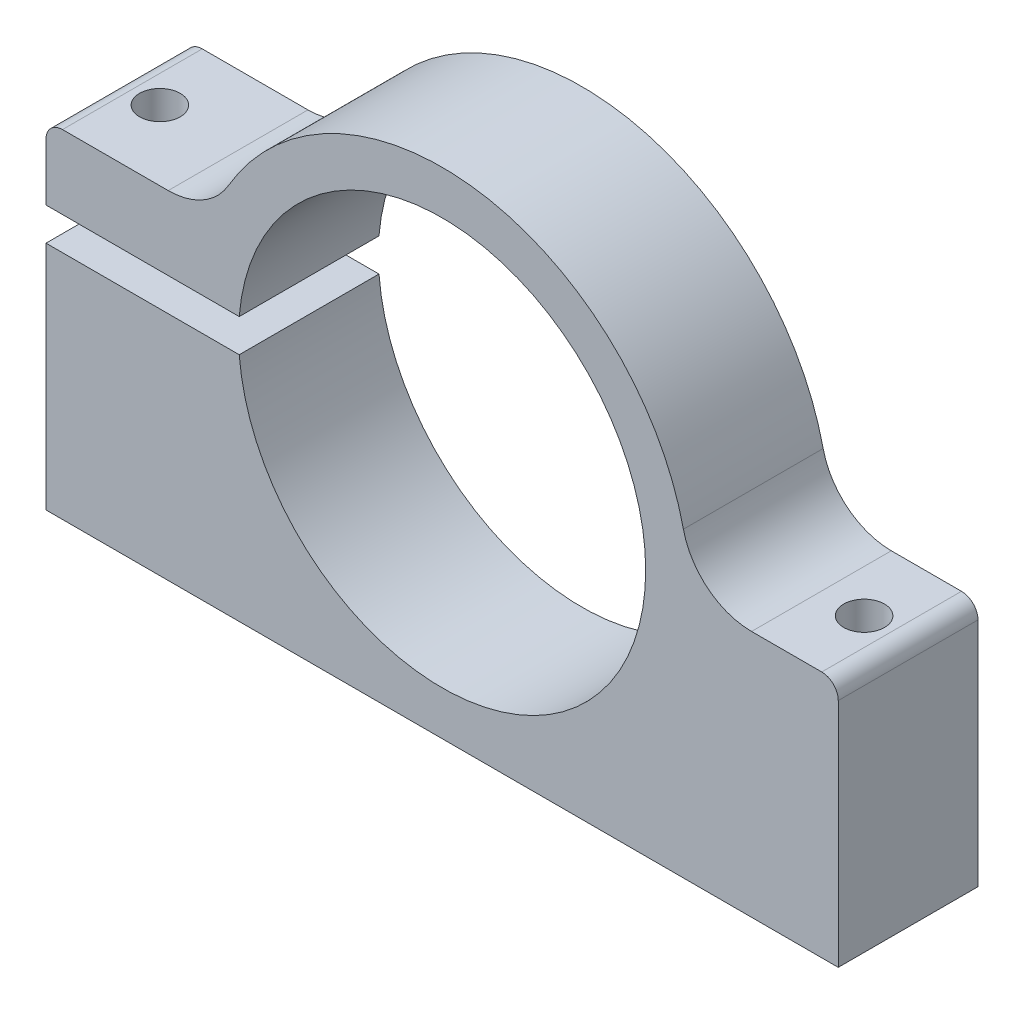
SolidWorks part; units mm, degrees
material "6061 Alloy"
ref_plane "Front Plane" through (0, 0, 0) normal (0, 0, 1) x (1, 0, 0)
ref_plane "Top Plane" through (0, 0, 0) normal (0, 1, 0) x (1, 0, 0)
ref_plane "Right Plane" through (0, 0, 0) normal (1, 0, 0) x (0, 0, -1)
sketch "Sketch1" plane through (0, 0, 0) normal (0, 0, 1) x (1, 0, 0)
  line L0 (0, 0) -> (0, -1.5)
  line L1 (-22.4299, -1.5) -> (-36, -1.5)
  line L2 (-36, -1.5) -> (-36, -22.5)
  line L3 (-36, -22.5) -> (36, -22.5)
  line L4 (36, -22.5) -> (36, 0)
  line L5 (36, 0) -> (22.48, 0)
  line L6 (0, 0) -> (0, 1.5)
  line L7 (-22.4299, 1.5) -> (-36, 1.5)
  line L8 (-36, 1.5) -> (-36, 8.191)
  line L9 (-36, 8.191) -> (-20.9346, 8.191)
  line L10 (-22.4299, 1.5) -> (-22.4299, -1.5)
  arc A0 (22.48, 0) -> (-20.9346, 8.191) centre (0, 0) ccw
  dimension "D1" = 44.96
  dimension "D2" = 36
  dimension "D3" = 36
  dimension "D4" = 21
  dimension "D5" = 1.5
  dimension "D6" = 36
  dimension "D7" = 1.5
extrude "Extrude1" add sketch "Sketch1" against normal blind 12.7 contours L1 L2 L3 L4 L5 A0 L9 L8 L7 L10
sketch "Sketch2" plane through (0, 0, 0) normal (0, 0, 1) x (1, 0, 0)
  circle A0 centre (0, 0) radius 18.5
  dimension "D1" = 37
extrude "Cut-Extrude1" cut sketch "Sketch2" against normal through all
sketch "Sketch4" plane through (0, 0, 0) normal (0, 0, 1) x (1, 0, 0)
  line L0 (-22.4299, 1.5) -> (-18.4391, 1.5)
  line L1 (-22.4299, 1.5) -> (-22.4299, -1.5)
  line L2 (-22.4299, -1.5) -> (-18.4391, -1.5)
  line L3 (-18.4391, -1.5) -> (-18.4391, 1.5)
  circle A0 centre (0, 0) radius 18.5 construction
extrude "Cut-Extrude2" cut sketch "Sketch4" against normal through all
sketch "Sketch5" plane through (0, 8.191, 0) normal (0, 1, 0) x (1, 0, 0)
  line L0 (-36, 12.7) -> (-20.9346, 12.7) construction
  circle A0 centre (-32, 6.35) radius 1.85
  dimension "D3" = 3.7
  dimension "D1" = 32
  dimension "D2" = 6.35
extrude "Cut-Extrude3" cut sketch "Sketch5" against normal through all
sketch "Sketch6" plane through (0, 0, 0) normal (0, 1, 0) x (1, 0, 0)
  line L0 (36, 0) -> (22.48, 0) construction
  circle A0 centre (32, 6.35) radius 1.85
  dimension "D1" = 3.7
  dimension "D2" = 32
  dimension "D3" = 6.35
extrude "Cut-Extrude4" cut sketch "Sketch6" against normal through all
fillet "Fillet2" radius 6.35 1 edges at (22.48, 0, -6.35)
fillet "Fillet3" radius 6.35 1 edges at (-20.9346, 8.191, -6.35)
fillet "Fillet6" radius 1.5 1 edges at (36, 0, -6.35)
fillet "Fillet7" radius 1.5 1 edges at (-36, 8.191, -6.35)
